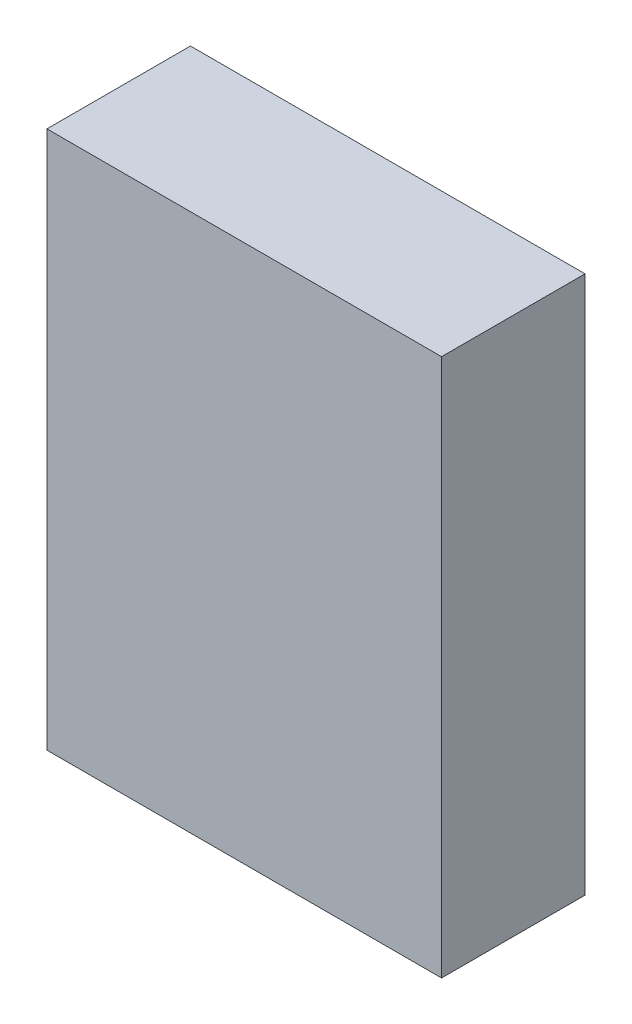
SolidWorks part; units mm, degrees
ref_plane "Plan de face" through (0, 0, 0) normal (0, 0, 1) x (1, 0, 0)
ref_plane "Plan de dessus" through (0, 0, 0) normal (0, 1, 0) x (1, 0, 0)
ref_plane "Plan de droite" through (0, 0, 0) normal (1, 0, 0) x (0, 0, -1)
sketch "Esquisse1" plane through (0, 0, 0) normal (0, 0, 1) x (1, 0, 0)
  line L1 (-52.7699, 39.8918) -> (57.2301, 39.8918)
  line L2 (-52.7699, 39.8918) -> (-52.7699, -110.1082)
  line L3 (-52.7699, -110.1082) -> (57.2301, -110.1082)
  line L4 (57.2301, 39.8918) -> (57.2301, -110.1082)
  dimension "D1" = 110
  dimension "D2" = 150
extrude "Boss.-Extru.1" add sketch "Esquisse1" along normal blind 40
